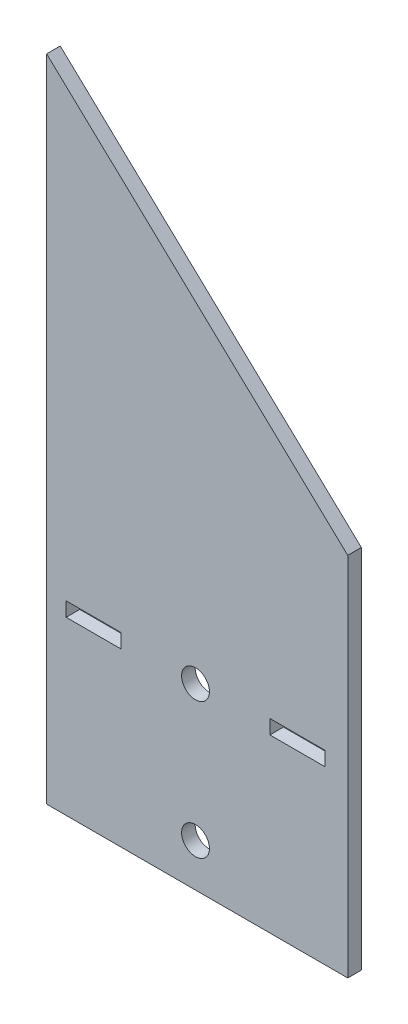
SolidWorks part; units mm, degrees
ref_plane "前视基准面" through (0, 0, 0) normal (0, 0, 1) x (1, 0, 0)
ref_plane "上视基准面" through (0, 0, 0) normal (0, 1, 0) x (1, 0, 0)
ref_plane "右视基准面" through (0, 0, 0) normal (1, 0, 0) x (0, 0, -1)
sketch "草图1" plane through (0, 0, 0) normal (0, 0, 1) x (1, 0, 0)
  line L0 (0, -35.4) -> (0, -15.4) construction
  line L1 (0, -15.4) -> (-15, -15.4) construction
  line L2 (0, -25.4) -> (-3.9018, -25.4) construction
  line L3 (-19.05, -14.35) -> (-10.95, -14.35)
  line L4 (-19.05, -14.35) -> (-19.05, -16.45)
  line L5 (-19.05, -16.45) -> (-10.95, -16.45)
  line L6 (-10.95, -14.35) -> (-10.95, -16.45)
  line L7 (-19.05, -14.35) -> (-10.95, -16.45) construction
  line L8 (-19.05, -16.45) -> (-10.95, -14.35) construction
  line L9 (10.95, -14.35) -> (10.95, -16.45)
  line L10 (19.05, -14.35) -> (10.95, -14.35)
  line L11 (19.05, -14.35) -> (19.05, -16.45)
  line L12 (19.05, -16.45) -> (10.95, -16.45)
  line L13 (-21.9187, -9.7878) -> (-21.9187, -41.7145)
  line L14 (-21.9187, -41.7145) -> (22.4194, -41.7145)
  line L15 (22.4194, -41.7145) -> (22.4194, -9.7878)
  line L16 (22.4194, -9.7878) -> (22.4194, 12.1881)
  line L17 (22.4194, 12.1881) -> (-21.9187, 53.9686)
  line L18 (-21.9187, 53.9686) -> (-21.9187, -9.7878)
  circle A0 centre (0, -35.4) radius 2.05
  circle A1 centre (0, -15.4) radius 2.05
  circle A6 centre (0, -15.4) radius 3.35 construction
  dimension "D1" = 4.1
  dimension "D3" = 4.1
  dimension "D11" = 6.7
  dimension "D2" = 20
  dimension "D4" = 15
  dimension "D5" = 8.1
  dimension "D6" = 2.1
extrude "凸台-拉伸1" add sketch "草图1" along normal blind 2
